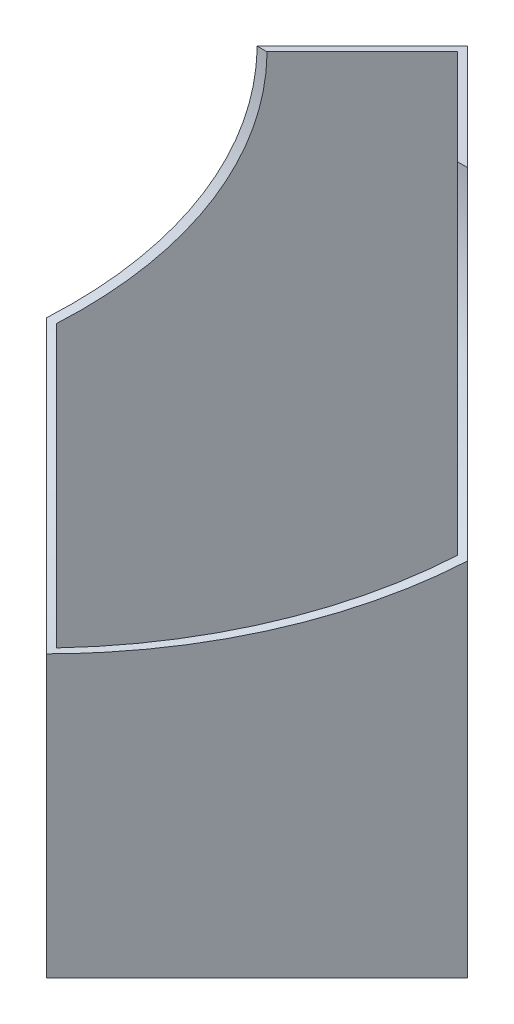
SolidWorks part; units mm, degrees
ref_plane "Front" through (0, 0, 0) normal (0, 0, 1) x (1, 0, 0)
ref_plane "Top" through (0, 0, 0) normal (0, 1, 0) x (1, 0, 0)
ref_plane "Right" through (0, 0, 0) normal (1, 0, 0) x (0, 0, -1)
sketch "Sketch1" plane through (0, 0, 0) normal (0, 1, 0) x (1, 0, 0)
  line L0 (0, 30) -> (30, 0)
  line L1 (30, 0) -> (0, -30)
  line L2 (0, -30) -> (-30, 0)
  line L3 (-30, 0) -> (0, 30)
extrude "Extrude1" add sketch "Sketch1" along normal blind 85
shell "Shell1" thickness 1
sketch "Sketch3" plane through (0, 0, 0) normal (1, 0, 0) x (0, 0, -1)
  circle A0 centre (-30, 85) radius 45
extrude "Cut-Extrude1" cut sketch "Sketch3" against normal mid plane 60
